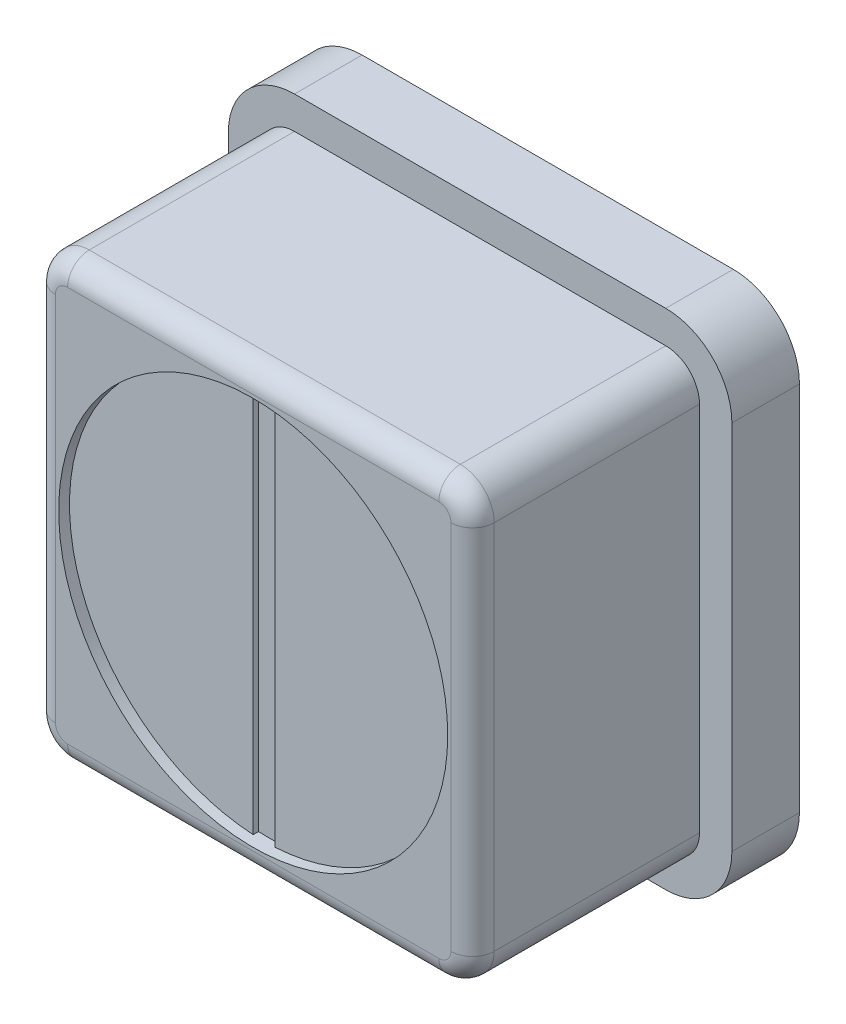
SolidWorks part; units mm, degrees
material "Nylon 101"
ref_plane "Front Plane" through (0, 0, 0) normal (0, 0, 1) x (1, 0, 0)
ref_plane "Top Plane" through (0, 0, 0) normal (0, 1, 0) x (1, 0, 0)
ref_plane "Right Plane" through (0, 0, 0) normal (1, 0, 0) x (0, 0, -1)
sketch "Sketch1" plane through (0, 0, 0) normal (0, 0, 1) x (1, 0, 0)
  line L0 (0, 0) -> (-5.1562, 0) construction
  line L4 (0, 5.1562) -> (0, -5.1562) construction
  line L8 (4.3624, 5.1562) -> (-4.3624, 5.1562)
  line L9 (-5.1562, 4.3625) -> (-5.1562, -4.3625)
  line L10 (-4.3624, -5.1562) -> (4.3624, -5.1562)
  line L11 (5.1562, -4.3624) -> (5.1562, 4.3624)
  arc A8 (-4.3624, 5.1562) -> (-5.1562, 4.3625) centre (-4.3624, 4.3624) ccw
  arc A9 (-5.1562, -4.3625) -> (-4.3624, -5.1562) centre (-4.3624, -4.3624) ccw
  arc A10 (4.3624, -5.1562) -> (5.1562, -4.3624) centre (4.3624, -4.3624) ccw
  arc A11 (5.1562, 4.3624) -> (4.3624, 5.1562) centre (4.3624, 4.3624) ccw
  point P6 (0, 0)
  dimension "D3" = 0.7938
  dimension "D2" = 1.1225
  dimension "D4" = 10.3124
  dimension "D1" = 10.3124
  dimension "D5" = 10.3124
extrude "Boss-Extrude1" add sketch "Sketch1" against normal blind 5.334
fillet "Fillet1" radius 0.508 8 edges at (5.1562, 0, 0) (4.9237, -4.9237, 0) (0, -5.1562, 0) (-4.9237, -4.9237, 0) (-5.1562, 0, 0) (-4.9237, 4.9237, 0) (0, 5.1562, 0) (4.9237, 4.9237, 0)
sketch "Sketch2" plane through (0, 0, 0) normal (0, 0, 1) x (1, 0, 0)
  line L0 (0, 0) -> (0, -5.1562) construction
  line L1 (4.3624, -5.1562) -> (-4.3624, -5.1562) construction
  line L2 (0, 0) -> (5.1562, 0) construction
  line L3 (5.1562, 4.3624) -> (5.1562, -4.3624) construction
  circle A0 centre (0, 0) radius 4.572
  dimension "D1" = 9.144
extrude "Cut-Extrude1" cut sketch "Sketch2" against normal blind 0.254
sketch "Sketch3" plane through (0, 0, -0.254) normal (0, 0, 1) x (1, 0, 0)
  line L0 (0, -4.572) -> (0, 4.572) construction
  line L1 (-0.254, -4.572) -> (-0.254, 4.572)
  line L2 (0.254, -4.572) -> (0.254, 4.572)
  line L3 (0.254, -4.572) -> (0.254, 4.572)
  circle A0 centre (0, 0) radius 4.572 construction
  circle A1 centre (0, 0) radius 4.572 construction
  arc A2 (-0.254, -4.5649) -> (0.254, -4.5649) centre (0, 0) ccw
  arc A3 (0.254, 4.5649) -> (-0.254, 4.5649) centre (0, 0) ccw
  point P9 (0, 0)
  dimension "D2" = 0.254
  dimension "D1" = 0.254
extrude "Cut-Extrude2" cut sketch "Sketch3" against normal blind 0.127
sketch "Sketch4" plane through (0, 0, -5.334) normal (0, 0, -1) x (-1, 0, 0)
  line L8 (-5.9182, 4.3624) -> (-5.9182, -4.3624)
  line L9 (-4.3624, -5.9182) -> (4.3624, -5.9182)
  line L10 (5.9182, -4.3625) -> (5.9182, 4.3625)
  line L11 (4.3624, 5.9182) -> (-4.3624, 5.9182)
  line L12 (-5.9182, 4.3624) -> (-5.9182, -4.3624)
  line L13 (-4.3624, -5.9182) -> (4.3624, -5.9182)
  line L14 (5.9182, -4.3625) -> (5.9182, 4.3625)
  line L15 (4.3624, 5.9182) -> (-4.3624, 5.9182)
  arc A8 (-4.3624, 5.9182) -> (-5.9182, 4.3624) centre (-4.3624, 4.3624) ccw
  arc A9 (-5.9182, -4.3624) -> (-4.3624, -5.9182) centre (-4.3624, -4.3624) ccw
  arc A10 (4.3624, -5.9182) -> (5.9182, -4.3625) centre (4.3624, -4.3624) ccw
  arc A11 (5.9182, 4.3625) -> (4.3624, 5.9182) centre (4.3624, 4.3624) ccw
  arc A12 (-4.3624, 5.9182) -> (-5.9182, 4.3624) centre (-4.3624, 4.3624) ccw
  arc A13 (-5.9182, -4.3624) -> (-4.3624, -5.9182) centre (-4.3624, -4.3624) ccw
  arc A14 (4.3624, -5.9182) -> (5.9182, -4.3625) centre (4.3624, -4.3624) ccw
  arc A15 (5.9182, 4.3625) -> (4.3624, 5.9182) centre (4.3624, 4.3624) ccw
  dimension "D1" = 0.762
extrude "Boss-Extrude2" add sketch "Sketch4" along normal blind 1.5875
hole_wizard "#56 (0.0465) Diameter Hole1" positions "Sketch6" profile "Sketch7" hole size "#56" standard "ANSI Inch"
sketch "Sketch6" plane through (0, 0, -6.9215) normal (0, 0, -1) x (-1, 0, 0)
  point P0 (0, 0)
sketch "Sketch7" plane through (0, 0, -6.9215) normal (1, 0, 0) x (0, 1, 0)
  line L0 (0, 0) -> (0, 5.08)
  line L1 (0, 5.08) -> (0.5905, 5.08)
  line L2 (0.5905, 5.08) -> (0.5905, 0)
  line L5 (0.5905, 0) -> (0, 0)
  line L10 (0, 5.08) -> (-0.5906, 5.08) construction
  line L11 (0, -6.35) -> (0, 107.95) construction
  dimension "Hole Dia." = 1.1811
  dimension "Hole Depth" = 5.08
  dimension "Drill Angle" = 180
equation "\"D2@Sketch3\"=\"D1@Sketch3\""
